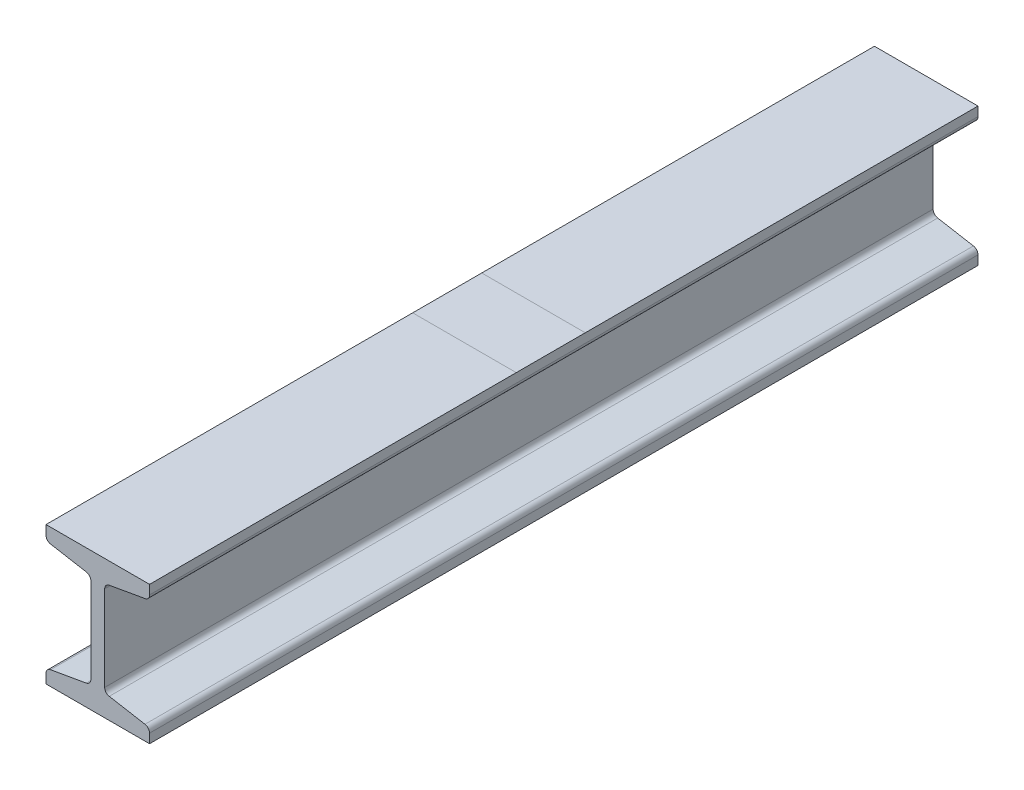
SolidWorks part; units mm, degrees
ref_plane "Front Plane" through (0, 0, 0) normal (0, 0, 1) x (1, 0, 0)
ref_plane "Top Plane" through (0, 0, 0) normal (0, 1, 0) x (1, 0, 0)
ref_plane "Right Plane" through (0, 0, 0) normal (1, 0, 0) x (0, 0, -1)
sketch "Sketch2" plane through (0, 0, 0) normal (0, 0, 1) x (1, 0, 0)
  line L0 (37.5, 50) -> (37.5, 40)
  line L1 (37.5, 40) -> (5, 34.2694)
  line L2 (5, 34.2694) -> (5, -34.2694)
  line L3 (5, -34.2694) -> (37.5, -40)
  line L4 (37.5, -40) -> (37.5, -50)
  line L5 (0, 0) -> (0, 44.375) construction
  line L6 (-37.5, -40) -> (-37.5, -50)
  line L7 (-5, -34.2694) -> (-37.5, -40)
  line L8 (-5, 34.2694) -> (-5, -34.2694)
  line L9 (-37.5, 40) -> (-5, 34.2694)
  line L10 (-37.5, 50) -> (-37.5, 40)
  line L11 (-37.5, 50) -> (37.5, 50)
  line L12 (-37.5, -50) -> (37.5, -50)
  line L13 (0, 0) -> (-6.8222, 0) construction
  dimension "D1" = 100
  dimension "D2" = 75
  dimension "D3" = 10
  dimension "D4" = 100
  dimension "D5" = 10
extrude "Boss-Extrude1" add sketch "Sketch2" along normal blind 600
fillet "Fillet1" radius 4 8 edges at (-37.5, -40, 300) (37.5, -40, 300) (-5, -34.2694, 300) (5, -34.2694, 300) (5, 34.2694, 300) (37.5, 40, 300) (-37.5, 40, 300) (-5, 34.2694, 300)
sketch "Sketch3" plane through (0, 50, 0) normal (0, 1, 0) x (1, 0, 0)
  line L0 (37.5, -600) -> (37.5, 0) construction
  line L1 (-37.5, -284.4268) -> (37.5, -284.4268)
  line L2 (-37.5, -284.4268) -> (-37.5, -334.4268)
  line L3 (-37.5, -334.4268) -> (37.5, -334.4268)
  line L4 (37.5, -284.4268) -> (37.5, -334.4268)
  line L5 (-37.5, -284.4268) -> (37.5, -334.4268) construction
  line L6 (-37.5, -334.4268) -> (37.5, -284.4268) construction
  point P0 (0, -309.4268)
  dimension "D1" = 50
  dimension "D2" = 75
split line "Split Line1"
sketch "Sketch4" plane through (0, -50, 0) normal (0, -1, 0) x (1, 0, 0)
  line L0 (37.5, 600) -> (37.5, 0) construction
  line L1 (-37.5, 600) -> (37.5, 600)
  line L2 (-37.5, 600) -> (-37.5, 560)
  line L3 (-37.5, 560) -> (37.5, 560)
  line L4 (37.5, 600) -> (37.5, 560)
  line L5 (-37.5, 600) -> (-37.5, 0) construction
  line L6 (37.5, 0) -> (-37.5, 0)
  line L7 (37.5, 0) -> (37.5, 40)
  line L8 (37.5, 40) -> (-37.5, 40)
  line L9 (-37.5, 0) -> (-37.5, 40)
  dimension "D1" = 40
  dimension "D2" = 40
split line "Split Line2"
